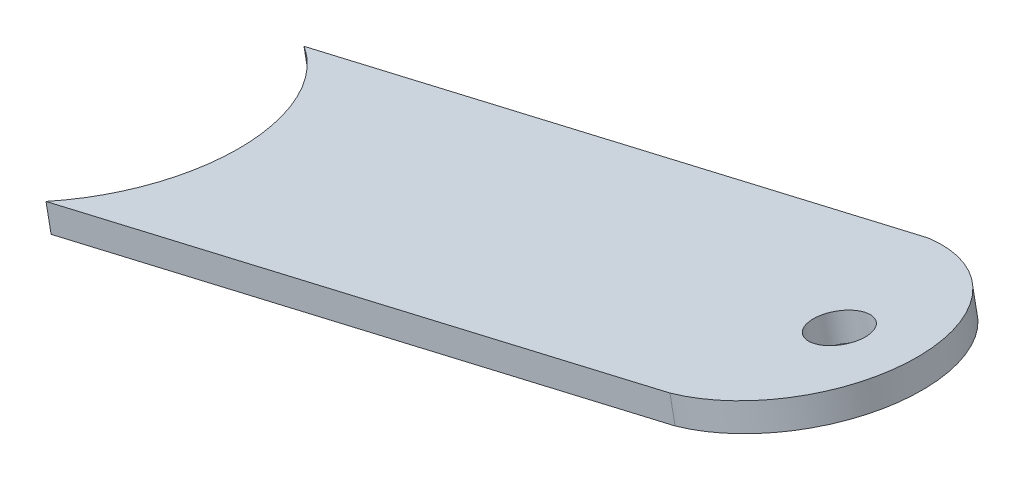
SolidWorks part; units mm, degrees
material "1.4105 (X6CrMoS17)"
ref_plane "Płaszczyzna XY" through (0, 0, 0) normal (0, 0, 1) x (1, 0, 0)
ref_plane "Płaszczyzna XZ" through (0, 0, 0) normal (0, 1, 0) x (1, 0, 0)
ref_plane "Płaszczyzna YZ" through (0, 0, 0) normal (1, 0, 0) x (0, 0, -1)
ref_plane "Płaszczyzna1" through (90.906, -464.0758, 0) normal (0.1922, -0.9813, 0) x (-0.9813, -0.1922, 0)
ref_plane "Płaszczyzna3" through (91.0022, -464.5665, 0) normal (0.1922, -0.9813, 0) x (-0.9813, -0.1922, 0)
sketch "Szkic1" plane through (91.0022, -464.5665, 0) normal (0.1922, -0.9813, 0) x (-0.9813, -0.1922, 0)
  line L0 (-852.6464, -589.8106) -> (-898.4127, -587.5725)
  line L2 (-852.1329, -569.8118) -> (-897.8992, -567.5737)
  arc A2 (-898.4127, -587.5725) -> (-897.8992, -567.5737) centre (-897.2356, -577.5967) cw
  spline S0 degree 3 poles (-850.3943, -568.7928) (-784.6601, -536.9278) (-774.2746, -609.2295) (-847.6891, -592.1634) knots -3.47317 -3.47317 -3.47317 -3.47317 4.445881 4.445881 4.445881 4.445881 weights 2.944007 0.319333 0.310319 2.916967 only from (-833.3706, -574.3894) to (-832.3981, -583.0409)
  spline S1 degree 3 poles (-842.1034, -592.2266) (-985.7209, -622.1994) (-945.1609, -488.8507) (-837.0118, -570.0734) knots -1.455639 -1.455639 -1.455639 -1.455639 2.4727 2.4727 2.4727 2.4727 weights 2.950176 0.155947 0.168135 2.986741 only from (-855.687, -586.4122) to (-851.9069, -569.6577)
  spline S2 degree 3 poles (-852.6464, -589.8106) (-859.5994, -584.423) (-860.0178, -575.3122) (-852.1329, -569.8118) knots -0.28909 -0.28909 -0.28909 -0.28909 0.984326 0.984326 0.984326 0.984326 weights 1.203316 0.837838 0.76726 0.991582
  dimension "D2" = 45.821
  dimension "D4" = 10.045
  dimension "D1" = 20
  dimension "D3" = 898.4127
  dimension "D5" = 577.5967
extrude "Dodanie-wyciągnięcie1" add sketch "Szkic1" along normal blind 1.5 and the other way blind 0.5
ref_plane "Płaszczyzna2" through (91.2905, -466.0385, 0) normal (0.1922, -0.9813, 0) x (-0.9813, -0.1922, 0)
sketch "Szkic2" plane through (91.2905, -466.0385, 0) normal (0.1922, -0.9813, 0) x (-0.9813, -0.1922, 0)
  line L0 (-898.4127, -587.5725) -> (-852.6464, -589.8106) construction
  circle A0 centre (-901.1177, -577.4282) radius 2
  dimension "D1" = 4
  dimension "D2" = 2.7051
  dimension "D3" = 10
extrude "Wytnij-wyciągnięcie1" cut sketch "Szkic2" against normal through all
